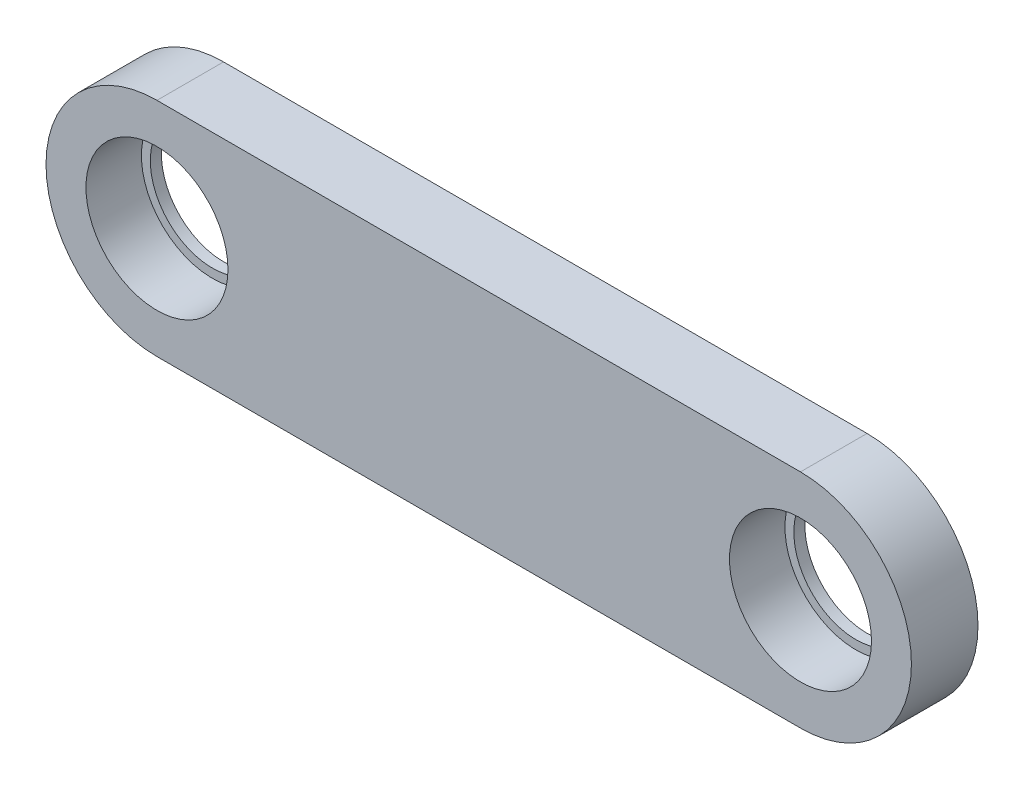
SolidWorks part; units mm, degrees
material "A3"
ref_plane "前视基准面" through (0, 0, 0) normal (0, 0, 1) x (1, 0, 0)
ref_plane "上视基准面" through (0, 0, 0) normal (0, 1, 0) x (1, 0, 0)
ref_plane "右视基准面" through (0, 0, 0) normal (1, 0, 0) x (0, 0, -1)
sketch "草图1" plane through (0, 0, 0) normal (0, 0, 1) x (1, 0, 0)
  line L0 (-123.7114, 0) -> (108.5571, 0) construction
  line L1 (0, 71.5457) -> (0, -64.26) construction
  line L2 (-72.5, 0) -> (72.5, 0) construction
  line L3 (-72.5, 25) -> (72.5, 25)
  line L4 (-72.5, -25) -> (72.5, -25)
  arc A0 (-72.5, 25) -> (-72.5, -25) centre (-72.5, 0) ccw
  arc A1 (72.5, -25) -> (72.5, 25) centre (72.5, 0) ccw
  point P7 (0, 0)
  dimension "D1" = 50
  dimension "D2" = 145
extrude "凸台-拉伸1" add sketch "草图1" along normal blind 15
sketch "草图2" plane through (0, 0, 15) normal (0, 0, 1) x (1, 0, 0)
  line L0 (-72.5, 25) -> (-72.5, -25) construction
  line L1 (-72.5, -25) -> (72.5, -25) construction
  line L2 (72.5, 25) -> (72.5, -25) construction
  circle A0 centre (-72.5, 0) radius 16
  circle A1 centre (72.5, 0) radius 16
  dimension "D1" = 32
extrude "切除-拉伸1" cut sketch "草图2" against normal blind 12.5
sketch "草图3" plane through (0, 0, 15) normal (0, 0, 1) x (1, 0, 0)
  circle A0 centre (-72.5, 0) radius 14
  circle A1 centre (72.5, 0) radius 14
  dimension "D1" = 28
extrude "切除-拉伸2" cut sketch "草图3" against normal through all and the other way through all
